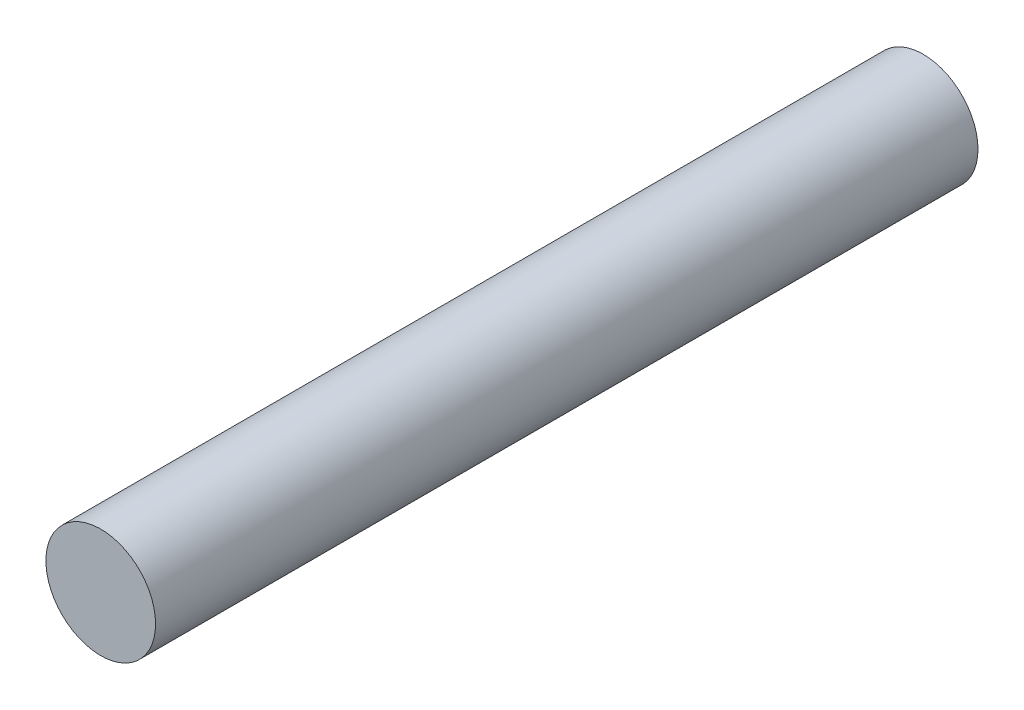
SolidWorks part; units mm, degrees
material "6063-T6"
ref_plane "Front Plane" through (0, 0, 0) normal (0, 0, 1) x (1, 0, 0)
ref_plane "Top Plane" through (0, 0, 0) normal (0, 1, 0) x (1, 0, 0)
ref_plane "Right Plane" through (0, 0, 0) normal (1, 0, 0) x (0, 0, -1)
sketch "Sketch1" plane through (0, 0, 0) normal (0, 0, 1) x (1, 0, 0)
  circle A0 centre (0, 0) radius 2.54
  dimension "D1" = 5.08
extrude "Boss-Extrude1" add sketch "Sketch1" along normal blind 38.1 contours A0
